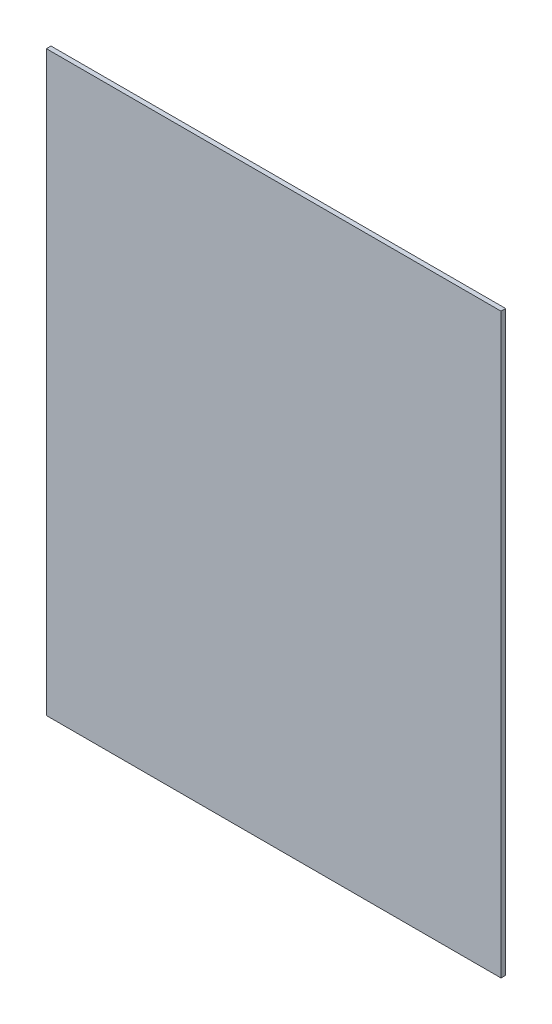
SolidWorks part; units mm, degrees
ref_plane "Front Plane" through (0, 0, 0) normal (0, 0, 1) x (1, 0, 0)
ref_plane "Top Plane" through (0, 0, 0) normal (0, 1, 0) x (1, 0, 0)
ref_plane "Right Plane" through (0, 0, 0) normal (1, 0, 0) x (0, 0, -1)
sketch "Sketch1" plane through (0, 0, 0) normal (0, 0, 1) x (1, 0, 0)
  line L0 (-35, 7.5) -> (-35, 97.5) construction
  line L1 (-35, 97.5) -> (35, 97.5) construction
  line L2 (35, 97.5) -> (35, 7.5) construction
  line L3 (35, 7.5) -> (-35, 7.5) construction
  line L4 (-35, 7.5) -> (-35, 97.5) construction
  line L5 (-35, 97.5) -> (35, 97.5) construction
  line L6 (35, 97.5) -> (35, 7.5) construction
  line L7 (35, 7.5) -> (-35, 7.5) construction
  line L8 (-37, 5.5) -> (-37, 99.5)
  line L9 (-37, 99.5) -> (37, 99.5)
  line L10 (37, 99.5) -> (37, 5.5)
  line L11 (37, 5.5) -> (-37, 5.5)
  dimension "D1" = 2
extrude "Boss-Extrude1" add sketch "Sketch1" along normal blind 0.75
